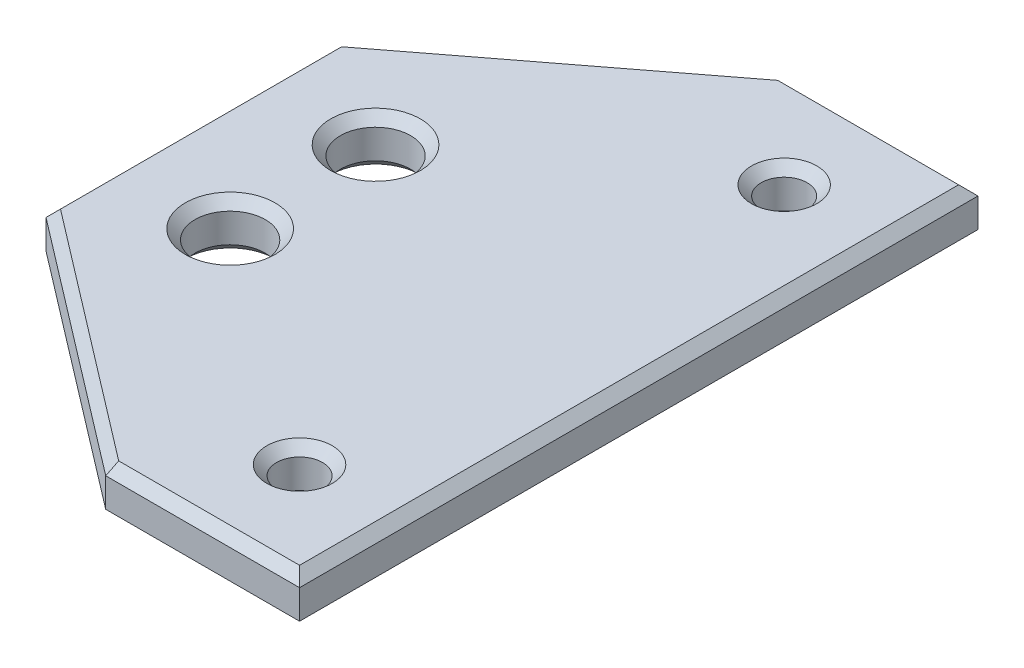
SolidWorks part; units mm, degrees
ref_plane "Plano frontal" through (0, 0, 0) normal (0, 0, 1) x (1, 0, 0)
ref_plane "Plano superior" through (0, 0, 0) normal (0, 1, 0) x (1, 0, 0)
ref_plane "Plano direito" through (0, 0, 0) normal (1, 0, 0) x (0, 0, -1)
sketch "Esboço1" plane through (0, 0, 0) normal (0, 1, 0) x (1, 0, 0)
  line L0 (-23.0809, -15) -> (3.0809, -35)
  line L1 (-23.0809, 15) -> (3.0809, 15)
  line L2 (-23.0809, 15) -> (-23.0809, -15)
  line L3 (-23.0809, -15) -> (3.0809, -15)
  line L4 (23.0809, 15) -> (23.0809, -15)
  line L5 (-23.0809, 15) -> (23.0809, -15) construction
  line L6 (-23.0809, -15) -> (23.0809, 15) construction
  line L7 (3.0809, 35) -> (-23.0809, 15)
  line L8 (23.0809, 15) -> (23.0809, 35)
  line L9 (23.0809, 35) -> (3.0809, 35)
  line L10 (3.0809, 15) -> (3.0809, 35)
  line L12 (23.0809, -15) -> (23.0809, -35)
  line L13 (23.0809, -35) -> (3.0809, -35)
  line L14 (3.0809, -15) -> (3.0809, -35)
  circle A0 centre (13.0809, 25) radius 2.375
  circle A1 centre (13.0809, -25) radius 2.375
  circle A2 centre (-11.5809, 7.5) radius 3.625
  circle A3 centre (-11.5809, -7.5) radius 3.625
  point P0 (0, 0)
  dimension "D1" = 7.25
  dimension "D2" = 4.75
  dimension "D3" = 4.75
  dimension "D4" = 7.25
  dimension "D5" = 15
  dimension "D6" = 7.5
  dimension "D9" = 30
  dimension "D10" = 11.5
  dimension "D11" = 20
  dimension "D12" = 20
  dimension "D13" = 20
  dimension "D14" = 20
  dimension "D7" = 10
  dimension "D8" = 10
  dimension "D15" = 10
  dimension "D16" = 10
extrude "Ressalto-extrusão1" add sketch "Esboço1" along normal blind 5 contours L3 L14 L13 L12 L4 L8 L9 L10 L1 L2 A3 A2 A1 A0 | L1 L10 L7 | L14 L3 L0
chamfer "Chanfro2" distance 1 angle 45 20 edges at (13.0809, 5, -22.625) (13.0809, 0, -22.625) (13.0809, 5, 27.375) (13.0809, 0, 27.375) (-11.5809, 5, -3.875) (-11.5809, 0, -3.875) (-11.5809, 5, 11.125) (-11.5809, 0, 11.125) (-10, 0, -25) (-10, 5, -25) (-23.0809, 0, 0) (-23.0809, 5, 0) (-10, 0, 25) (-10, 5, 25) (13.0809, 0, 35) (13.0809, 5, 35) (23.0809, 0, 0) (23.0809, 5, 0) (13.0809, 0, -35) (13.0809, 5, -35)
sketch "Esboço2" plane through (0, 0, 0) normal (0, -1, 0) x (1, 0, 0)
  line L0 (13.0809, 25) -> (13.0809, -25) construction
  line L2 (10.0809, 17) -> (16.0809, 17)
  line L3 (10.0809, 17) -> (10.0809, -17)
  line L4 (10.0809, -17) -> (16.0809, -17)
  line L5 (16.0809, 17) -> (16.0809, -17)
  line L6 (10.0809, 17) -> (16.0809, -17) construction
  line L7 (10.0809, -17) -> (16.0809, 17) construction
  point P2 (13.0809, 0)
  dimension "D1" = 6
  dimension "D2" = 8
extrude "Ressalto-extrusão2" add sketch "Esboço2" along normal blind 2
equation "\"D3@Esboço1\"=\"D2@Esboço1\""
equation "\"D4@Esboço1\"=\"D1@Esboço1\""
equation "\"D6@Esboço1\"=\"D5@Esboço1\"/2"
equation "\"D11@Esboço1\"=\"D12@Esboço1\""
equation "\"D13@Esboço1\"=\"D12@Esboço1\""
equation "\"D14@Esboço1\"=\"D12@Esboço1\""
equation "\"D7@Esboço1\"=\"D12@Esboço1\"/2"
equation "\"D8@Esboço1\"=\"D7@Esboço1\""
equation "\"D15@Esboço1\"=\"D8@Esboço1\""
equation "\"D16@Esboço1\"=\"D8@Esboço1\""
